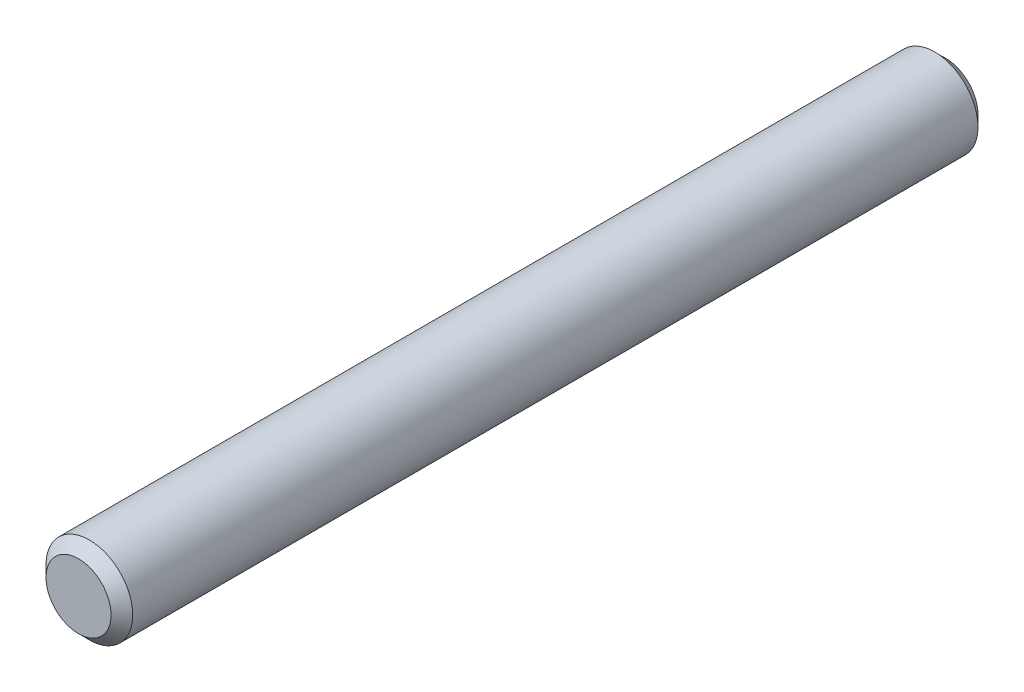
SolidWorks part; units mm, degrees
ref_plane "Płaszczyzna przednia" through (0, 0, 0) normal (0, 0, 1) x (1, 0, 0)
ref_plane "Płaszczyzna górna" through (0, 0, 0) normal (0, 1, 0) x (1, 0, 0)
ref_plane "Płaszczyzna prawa" through (0, 0, 0) normal (1, 0, 0) x (0, 0, -1)
sketch "Szkic1" plane through (0, 0, 0) normal (0, 0, 1) x (1, 0, 0)
  circle A0 centre (0, 0) radius 4
  dimension "D1" = 8
extrude "Dodanie-wyciągnięcie1" add sketch "Szkic1" along normal mid plane 80
chamfer "Sfazowanie1" distance 1 angle 45 2 edges at (4, 0, -40) (4, 0, 40)
